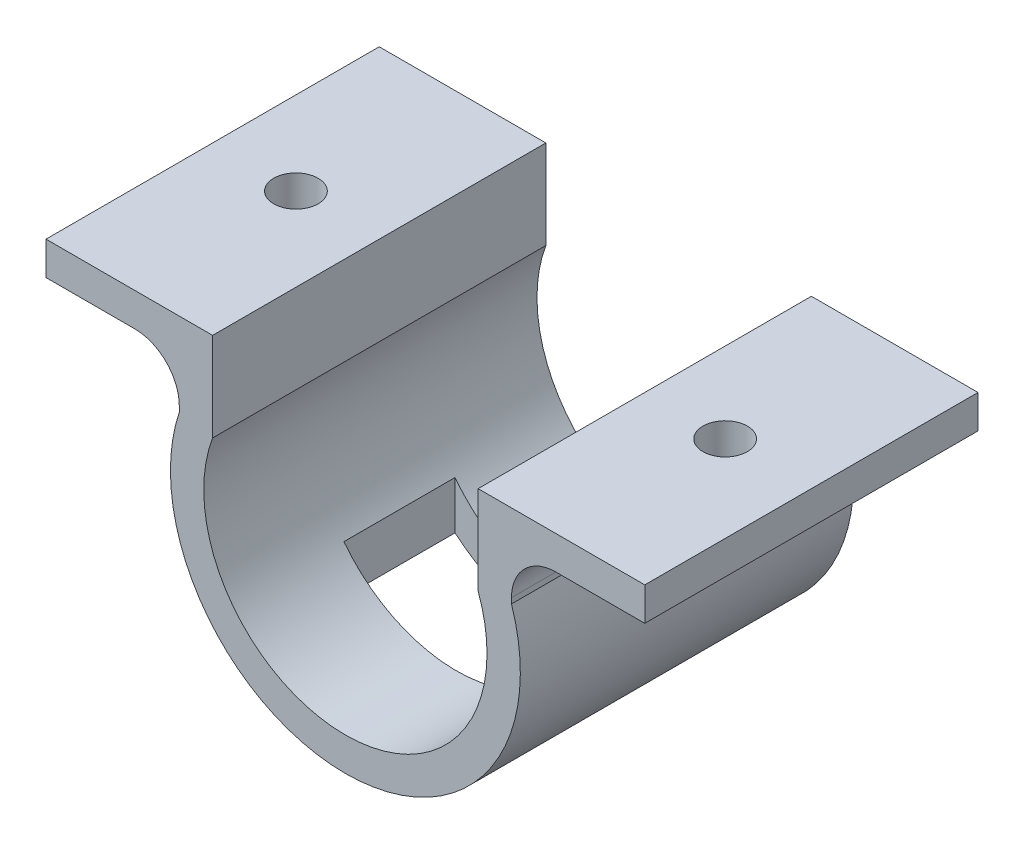
SolidWorks part; units mm, degrees
material "Rubber"
ref_plane "Front Plane" through (0, 0, 0) normal (0, 0, 1) x (1, 0, 0)
ref_plane "Top Plane" through (0, 0, 0) normal (0, 1, 0) x (1, 0, 0)
ref_plane "Right Plane" through (0, 0, 0) normal (1, 0, 0) x (0, 0, -1)
sketch "Sketch1" plane through (0, 0, 0) normal (0, 0, 1) x (1, 0, 0)
  line L0 (-11.8213, 4.4359) -> (-11.8213, 12.4359)
  line L1 (-11.8213, 12.4359) -> (-26.8213, 12.4359)
  line L2 (-11.8213, 4.4359) -> (12.0856, 4.4359) construction
  line L3 (0.1321, 0) -> (0.1321, 6.7441) construction
  line L4 (12.0856, 12.4359) -> (27.0856, 12.4359)
  line L5 (12.0856, 4.4359) -> (12.0856, 12.4359)
  arc A0 (-11.8213, 4.4359) -> (12.0856, 4.4359) centre (0.1321, 0) ccw
  dimension "D1" = 12.75
  dimension "D2" = 15
  dimension "D3" = 8
extrude "Extrude-Thin1" add sketch "Sketch1" along normal mid plane 30 thin thin type one direction wall 3
fillet "Fillet1" radius 4 2 edges at (15.0856, 9.4359, 0) (-14.8213, 9.4359, 0)
sketch "Sketch2" plane through (0, 12.4359, 0) normal (0, 1, 0) x (1, 0, 0)
  line L0 (-19.3213, 0) -> (19.3213, 0) construction
  line L2 (-26.8213, 15) -> (-11.8213, 15) construction
  point P3 (0, 0)
  point P4 (-19.3213, 15)
sketch "Sketch6" plane through (0, 12.4359, 0) normal (0, 1, 0) x (1, 0, 0)
  line L1 (-10, -5) -> (10, -5)
  line L2 (-10, -5) -> (-10, 5)
  line L3 (-10, 5) -> (10, 5)
  line L4 (10, -5) -> (10, 5)
  line L5 (-10, -5) -> (10, 5) construction
  line L6 (-10, 5) -> (10, -5) construction
  circle A0 centre (-19.3213, 0) radius 2
  circle A1 centre (19.3213, 0) radius 2
  point P0 (0, 0)
  dimension "D3" = 4
  dimension "D1" = 20
  dimension "D2" = 10
extrude "Cut-Extrude4" cut sketch "Sketch6" against normal through all
